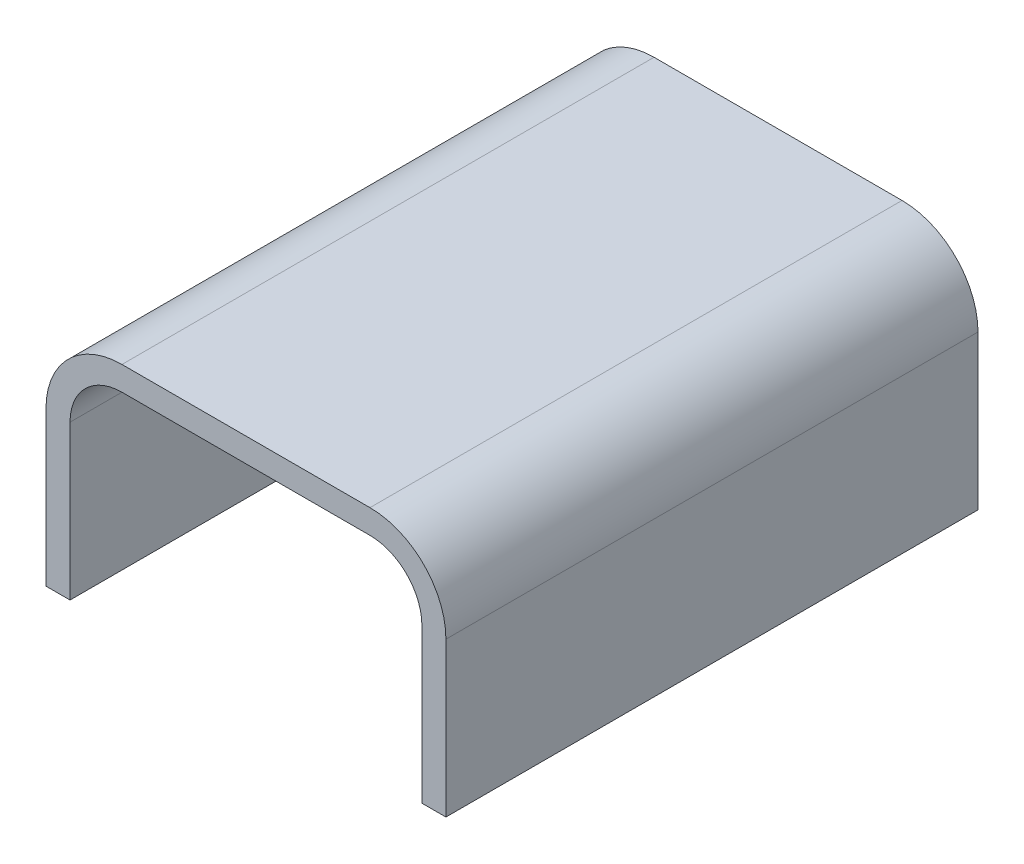
SolidWorks part; units mm, degrees
material "PVC Rigid"
ref_plane "Front Plane" through (0, 0, 0) normal (0, 0, 1) x (1, 0, 0)
ref_plane "Top Plane" through (0, 0, 0) normal (0, 1, 0) x (1, 0, 0)
ref_plane "Right Plane" through (0, 0, 0) normal (1, 0, 0) x (0, 0, -1)
sketch "Sketch2" plane through (0, 0, 0) normal (0, 0, 1) x (1, 0, 0)
  line L0 (0, 0) -> (0, 8.975)
  line L2 (3.025, 12) -> (17.475, 12)
  line L4 (20.5, 8.975) -> (20.5, 0)
  line L6 (-1.4, 0) -> (-1.4, 8.975)
  line L7 (3.025, 13.4) -> (17.475, 13.4)
  line L8 (21.9, 8.975) -> (21.9, 0)
  line L9 (-1.4, 0) -> (0, 0)
  line L10 (20.5, 0) -> (21.9, 0)
  arc A0 (3.025, 12) -> (0, 8.975) centre (3.025, 8.975) ccw
  arc A1 (20.5, 8.975) -> (17.475, 12) centre (17.475, 8.975) ccw
  arc A2 (3.025, 13.4) -> (-1.4, 8.975) centre (3.025, 8.975) ccw
  arc A3 (21.9, 8.975) -> (17.475, 13.4) centre (17.475, 8.975) ccw
  dimension "D1" = 6.05
  dimension "D2" = 6.05
  dimension "D3" = 1.4
extrude "Extrude1" add sketch "Sketch2" along normal blind 31
